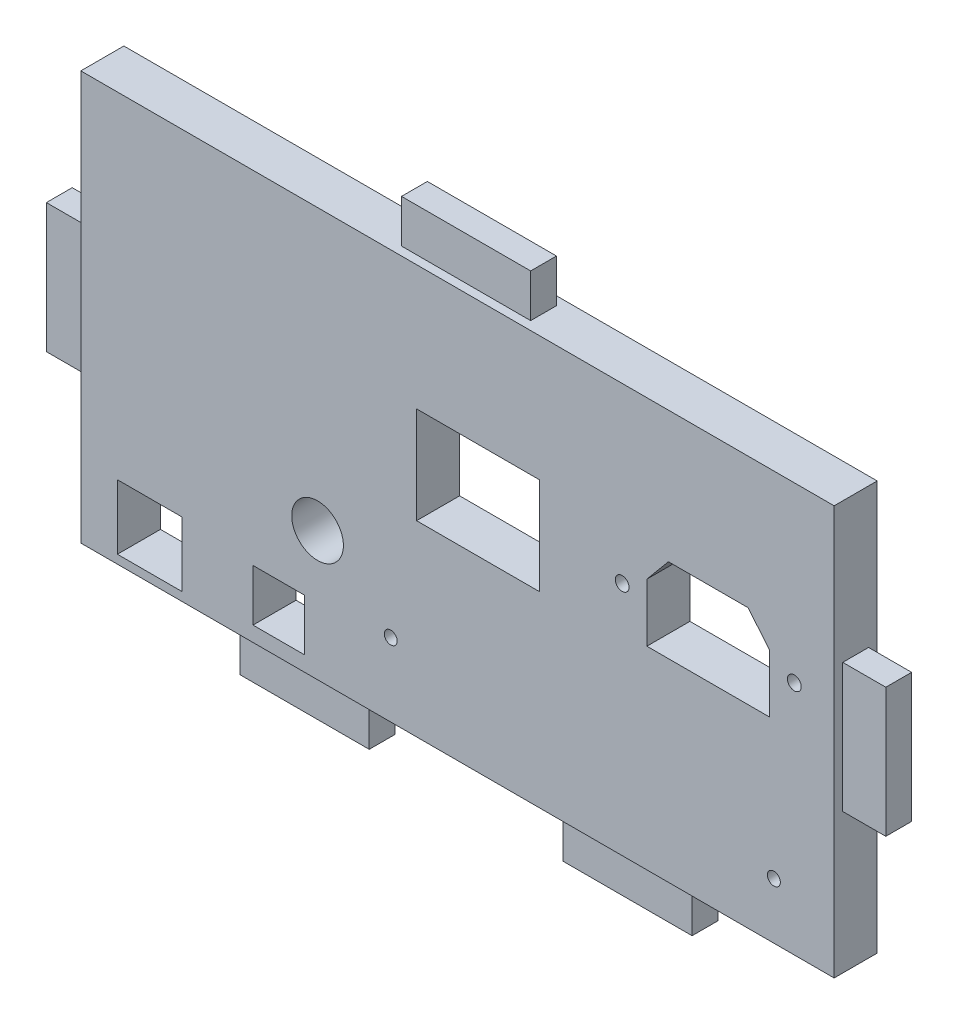
SolidWorks part; units mm, degrees
ref_plane "Plano frontal" through (0, 0, 0) normal (0, 0, 1) x (1, 0, 0)
ref_plane "Plano superior" through (0, 0, 0) normal (0, 1, 0) x (1, 0, 0)
ref_plane "Plano direito" through (0, 0, 0) normal (1, 0, 0) x (0, 0, -1)
sketch "Esboço1" plane through (0, 0, 0) normal (0, 0, 1) x (1, 0, 0)
  line L1 (87.5, -47.5) -> (-87.5, -47.5)
  line L2 (87.5, -47.5) -> (87.5, 47.5)
  line L3 (87.5, 47.5) -> (-87.5, 47.5)
  line L4 (-87.5, -47.5) -> (-87.5, 47.5)
  line L5 (87.5, -47.5) -> (-87.5, 47.5) construction
  line L6 (87.5, 47.5) -> (-87.5, -47.5) construction
  point P0 (0, 0)
  dimension "D1" = 95
  dimension "D2" = 175
extrude "Ressalto-extrusão1" add sketch "Esboço1" along normal blind 10
sketch "Esboço2" plane through (-87.5, 0, 0) normal (-1, 0, 0) x (0, 0, 1)
  line L0 (5, 47.5) -> (5, -47.5) construction
  line L1 (10, 47.5) -> (0, 47.5) construction
  line L2 (10, -47.5) -> (0, -47.5) construction
  line L3 (10, 0) -> (0, 0) construction
  line L4 (10, 47.5) -> (10, -47.5) construction
  line L6 (8, -15) -> (2, -15)
  line L7 (8, -15) -> (8, 15)
  line L8 (8, 15) -> (2, 15)
  line L9 (2, -15) -> (2, 15)
  line L10 (8, -15) -> (2, 15) construction
  line L11 (8, 15) -> (2, -15) construction
  point P11 (5, 0)
  dimension "D1" = 30
  dimension "D2" = 6
extrude "Ressalto-extrusão2" add sketch "Esboço2" along normal blind 10
sketch "Esboço3" plane through (87.5, 0, 0) normal (1, 0, 0) x (0, 0, -1)
  line L0 (-5, 50.9763) -> (-5, -49.5797) construction
  line L1 (0, 0) -> (-10, 0) construction
  line L2 (-10, -47.5) -> (-10, 47.5) construction
  line L4 (-8, -15) -> (-2, -15)
  line L5 (-8, -15) -> (-8, 15)
  line L6 (-8, 15) -> (-2, 15)
  line L7 (-2, -15) -> (-2, 15)
  line L8 (-8, -15) -> (-2, 15) construction
  line L9 (-8, 15) -> (-2, -15) construction
  point P7 (-5, 0)
  dimension "D1" = 6
  dimension "D2" = 30
extrude "Ressalto-extrusão3" add sketch "Esboço3" along normal blind 10
sketch "Esboço4" plane through (0, -47.5, 0) normal (0, -1, 0) x (1, 0, 0)
  line L0 (-87.5, 5) -> (87.5, 5) construction
  line L1 (-87.5, 10) -> (-87.5, 0) construction
  line L2 (87.5, 8) -> (87.5, 2) construction
  line L3 (0, 10) -> (0, 0) construction
  line L4 (-87.5, 10) -> (87.5, 10) construction
  line L5 (22.5, 8) -> (52.5, 8)
  line L6 (-22.5, 2) -> (-52.5, 2)
  line L7 (-22.5, 2) -> (-22.5, 8)
  line L8 (-22.5, 8) -> (-52.5, 8)
  line L9 (-52.5, 2) -> (-52.5, 8)
  line L10 (-22.5, 2) -> (-52.5, 8) construction
  line L11 (-22.5, 8) -> (-52.5, 2) construction
  line L12 (52.5, 2) -> (52.5, 8)
  line L13 (22.5, 2) -> (52.5, 2)
  line L14 (22.5, 2) -> (22.5, 8)
  line L15 (-87.5, 2) -> (-87.5, 8) construction
  point P11 (-37.5, 5)
  dimension "D1" = 30
  dimension "D2" = 6
  dimension "D3" = 50
extrude "Ressalto-extrusão4" add sketch "Esboço4" along normal blind 10
sketch "Esboço5" plane through (0, 47.5, 0) normal (0, 1, 0) x (1, 0, 0)
  line L0 (0, 0) -> (0, -10) construction
  line L1 (87.5, -10) -> (-87.5, -10) construction
  line L2 (-87.5, -5) -> (87.5, -5) construction
  line L3 (-87.5, -10) -> (-87.5, 0) construction
  line L4 (87.5, -10) -> (87.5, 0) construction
  line L6 (15, -8) -> (-15, -8)
  line L7 (15, -8) -> (15, -2)
  line L8 (15, -2) -> (-15, -2)
  line L9 (-15, -8) -> (-15, -2)
  line L10 (15, -8) -> (-15, -2) construction
  line L11 (15, -2) -> (-15, -8) construction
  point P11 (0, -5)
  dimension "D1" = 30
  dimension "D2" = 6
extrude "Ressalto-extrusão5" add sketch "Esboço5" along normal blind 10
sketch "Esboço7" plane through (0, 0, 10) normal (0, 0, 1) x (1, 0, 0)
  line L0 (87.5, -47.5) -> (87.5, 47.5) construction
  line L1 (-87.5, -47.5) -> (87.5, -47.5) construction
  line L2 (58.25, -3.9725) -> (58.25, 4.25) construction
  line L3 (72.5, -2.5) -> (44, -2.5)
  line L4 (72.5, -2.5) -> (72.5, 11)
  line L6 (44, -2.5) -> (44, 11)
  line L7 (72.5, -2.5) -> (44, 11) construction
  line L8 (72.5, 11) -> (44, -2.5) construction
  line L9 (49, 17) -> (67.5, 17)
  line L10 (49, 17) -> (44, 11)
  line L11 (67.5, 17) -> (72.5, 11)
  line L12 (58.25, 11) -> (58.25, 18.719) construction
  line L13 (114.0787, 7.25) -> (-14.7623, 7.25) construction
  line L14 (87.5, 15) -> (87.5, -15) construction
  line L15 (19, -4) -> (-9.5, -4)
  line L16 (19, -4) -> (19, 18.5)
  line L17 (19, 18.5) -> (-9.5, 18.5)
  line L18 (-9.5, -4) -> (-9.5, 18.5)
  line L19 (19, -4) -> (-9.5, 18.5) construction
  line L20 (19, 18.5) -> (-9.5, -4) construction
  line L21 (-87.5, 47.5) -> (-87.5, -47.5) construction
  line L22 (-79, -45.5) -> (-64, -45.5)
  line L23 (-79, -45.5) -> (-79, -30.5)
  line L24 (-79, -30.5) -> (-64, -30.5)
  line L25 (-64, -45.5) -> (-64, -30.5)
  line L26 (-79, -45.5) -> (-64, -30.5) construction
  line L27 (-79, -30.5) -> (-64, -45.5) construction
  line L29 (-35.5, -44) -> (-47.5, -44)
  line L30 (-35.5, -44) -> (-35.5, -32)
  line L31 (-35.5, -32) -> (-47.5, -32)
  line L32 (-47.5, -44) -> (-47.5, -32)
  line L33 (-35.5, -44) -> (-47.5, -32) construction
  line L34 (-35.5, -32) -> (-47.5, -44) construction
  circle A0 centre (73.5, -34.5) radius 1.5
  circle A1 centre (-15.5, -30.5) radius 1.5
  circle A2 centre (78.25, 7.25) radius 1.6
  circle A3 centre (38.25, 7.25) radius 1.6
  circle A4 centre (-32.5, -17.5) radius 6
  point P8 (58.25, 4.25)
  point P17 (58.25, 17)
  point P26 (4.75, 7.25)
  point P33 (-71.5, -38)
  point P40 (-41.5, -38)
  dimension "D1" = 3
  dimension "D2" = 14
  dimension "D3" = 13
  dimension "D4" = 103
  dimension "D5" = 17
  dimension "D10" = 5.75
  dimension "D11" = 9.75
  dimension "D25" = 55
  dimension "D26" = 12
  dimension "D27" = 30
  dimension "D6" = 13.5
  dimension "D7" = 28.5
  dimension "D8" = 18.5
  dimension "D9" = 19.5
  dimension "D12" = 45
  dimension "D13" = 28.5
  dimension "D14" = 22.5
  dimension "D15" = 15
  dimension "D16" = 25
  dimension "D17" = 16
  dimension "D18" = 15
  dimension "D19" = 15
  dimension "D20" = 9.5
  dimension "D21" = 12
  dimension "D22" = 12
  dimension "D23" = 9.5
  dimension "D24" = 30
  dimension "D28" = 14.25
extrude "Corte-extrusão2" cut sketch "Esboço7" against normal blind 10
